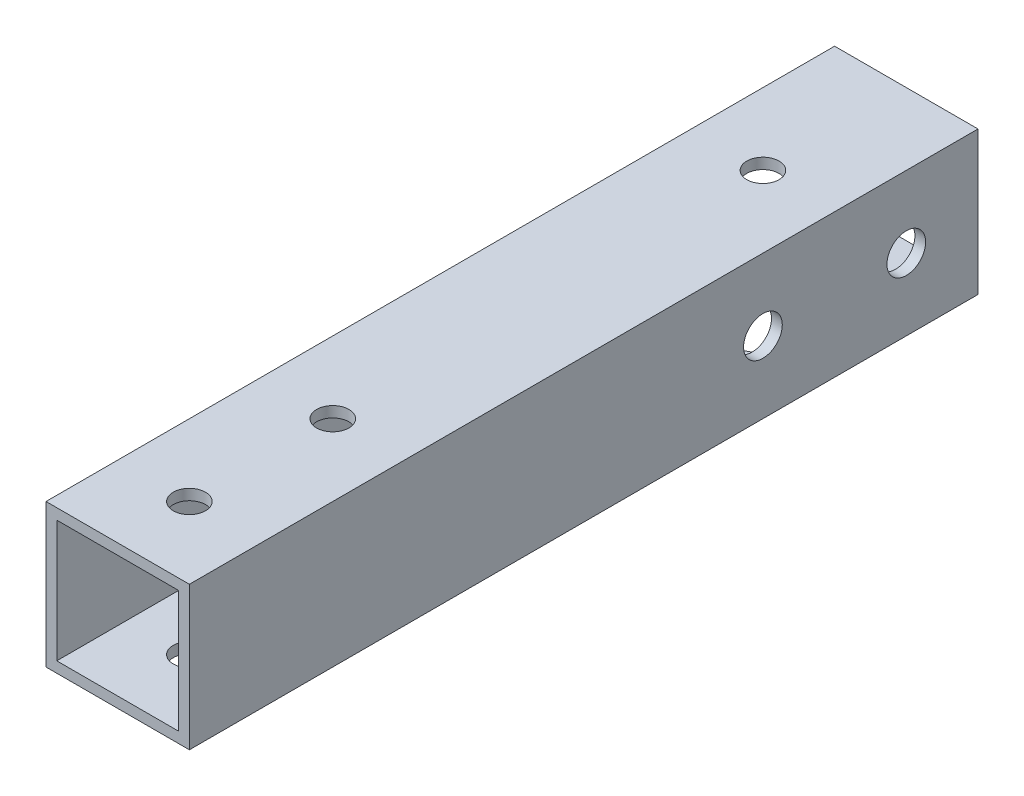
SolidWorks part; units mm, degrees
material "1060 合金"
ref_plane "正面" through (0, 0, 0) normal (0, 0, 1) x (1, 0, 0)
ref_plane "平面" through (0, 0, 0) normal (0, 1, 0) x (1, 0, 0)
ref_plane "右側面" through (0, 0, 0) normal (1, 0, 0) x (0, 0, -1)
sketch "ｽｹｯﾁ1" plane through (0, 0, 0) normal (0, 0, 1) x (1, 0, 0)
  line L1 (-10, -10) -> (10, -10)
  line L2 (-10, -10) -> (-10, 10)
  line L3 (-10, 10) -> (10, 10)
  line L4 (10, -10) -> (10, 10)
  line L5 (-10, -10) -> (10, 10) construction
  line L6 (-10, 10) -> (10, -10) construction
  line L7 (-8.5, -8.5) -> (8.5, -8.5)
  line L8 (-8.5, -8.5) -> (-8.5, 8.5)
  line L9 (-8.5, 8.5) -> (8.5, 8.5)
  line L10 (8.5, -8.5) -> (8.5, 8.5)
  line L11 (-8.5, -8.5) -> (8.5, 8.5) construction
  line L12 (-8.5, 8.5) -> (8.5, -8.5) construction
  point P0 (0, 0)
  point P6 (0, 0)
  dimension "D1" = 1.5
  dimension "D2" = 20
  dimension "D3" = 20
extrude "ﾎﾞｽ - 押し出し1" add sketch "ｽｹｯﾁ1" along normal blind 110
sketch "ｽｹｯﾁ2" plane through (10, 0, 0) normal (1, 0, 0) x (0, 0, -1)
  line L0 (-110, -10) -> (0, -10) construction
  circle A9 centre (-30, 0) radius 2.7
  circle A10 centre (-10, 0) radius 2.7
  dimension "D1" = 20
  dimension "D6" = 5.4
  dimension "D8" = 5.4
  dimension "D4" = 10
  dimension "D5" = 10
  dimension "D9" = 10
extrude "ｶｯﾄ - 押し出し1" cut sketch "ｽｹｯﾁ2" against normal blind 25
sketch "ｽｹｯﾁ3" plane through (0, 10, 0) normal (0, 1, 0) x (1, 0, 0)
  line L0 (10, -110) -> (-10, -110) construction
  line L1 (-10, -110) -> (-10, 0) construction
  circle A0 centre (0, -100) radius 2.25
  circle A4 centre (0, -80) radius 2.25
  circle A5 centre (0, -20) radius 2.25
  dimension "D1" = 4.5
  dimension "D2" = 10
  dimension "D3" = 10
  dimension "D6" = 2
  dimension "D7" = 20
  dimension "D5" = 20
  dimension "D4" = 2
extrude "ｶｯﾄ - 押し出し2" cut sketch "ｽｹｯﾁ3" against normal blind 20
sketch "ｽｹｯﾁ4" plane through (0, -10, 0) normal (0, -1, 0) x (-1, 0, 0)
  line L0 (10, 0) -> (-10, 0) construction
  circle A1 centre (0, -7.5) radius 2.25
  dimension "D2" = 7.5
  dimension "D6" = 4.5
extrude "ｶｯﾄ - 押し出し3" cut sketch "ｽｹｯﾁ4" against normal blind 5
sketch "ｽｹｯﾁ5" plane through (0, -10, 0) normal (0, -1, 0) x (-1, 0, 0)
  circle A0 centre (0, -20) radius 5
  dimension "D1" = 10
extrude "ｶｯﾄ - 押し出し4" cut sketch "ｽｹｯﾁ5" against normal blind 10
sketch "ｽｹｯﾁ6" plane through (10, 0, 0) normal (1, 0, 0) x (0, 0, -1)
  circle A0 centre (-10, 0) radius 5
  circle A1 centre (-30, 0) radius 5
  dimension "D1" = 10
  dimension "D2" = 10
extrude "ｶｯﾄ - 押し出し5" cut sketch "ｽｹｯﾁ6" against normal blind 10 from offset 10
